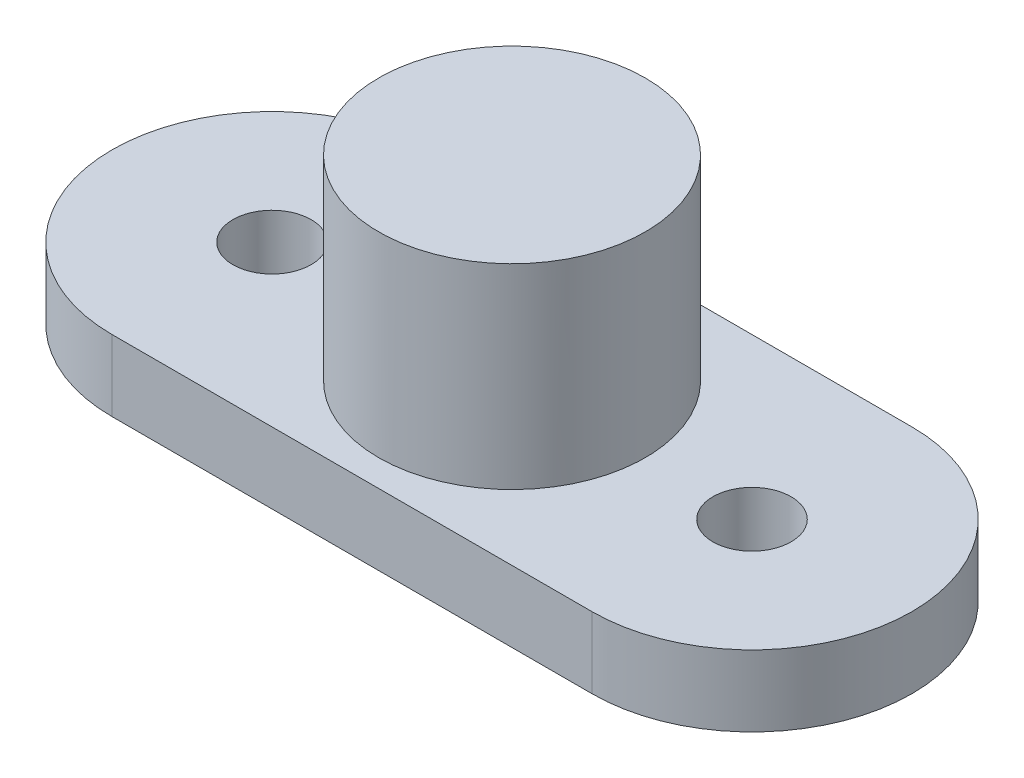
SolidWorks part; units mm, degrees
ref_plane "Front Plane" through (0, 0, 0) normal (0, 0, 1) x (1, 0, 0)
ref_plane "Top Plane" through (0, 0, 0) normal (0, 1, 0) x (1, 0, 0)
ref_plane "Right Plane" through (0, 0, 0) normal (1, 0, 0) x (0, 0, -1)
sketch "Sketch1" plane through (0, 0, 0) normal (0, 1, 0) x (1, 0, 0)
  line L0 (0, 0) -> (6.75, 0)
  line L1 (0, 0) -> (-6.75, 0)
  line L2 (-6.75, 4.4995) -> (6.75, 4.4995)
  line L3 (-6.75, -4.4995) -> (6.75, -4.4995)
  circle A0 centre (-6.75, 0) radius 1.1
  circle A1 centre (6.75, 0) radius 1.1
  arc A2 (6.75, 4.4995) -> (6.75, -4.4995) centre (6.75, 0) cw
  arc A3 (-6.75, 4.4995) -> (-6.75, -4.4995) centre (-6.75, 0) ccw
  circle A6 centre (0, 0) radius 3.75
extrude "Boss-Extrude3" add sketch "Sketch1" along normal blind 2
sketch "Sketch3" plane through (0, 0, 0) normal (0, -1, 0) x (1, 0, 0)
  circle A2 centre (0, 0) radius 3.75
extrude "Boss-Extrude4" add sketch "Sketch3" against normal blind 7.5
